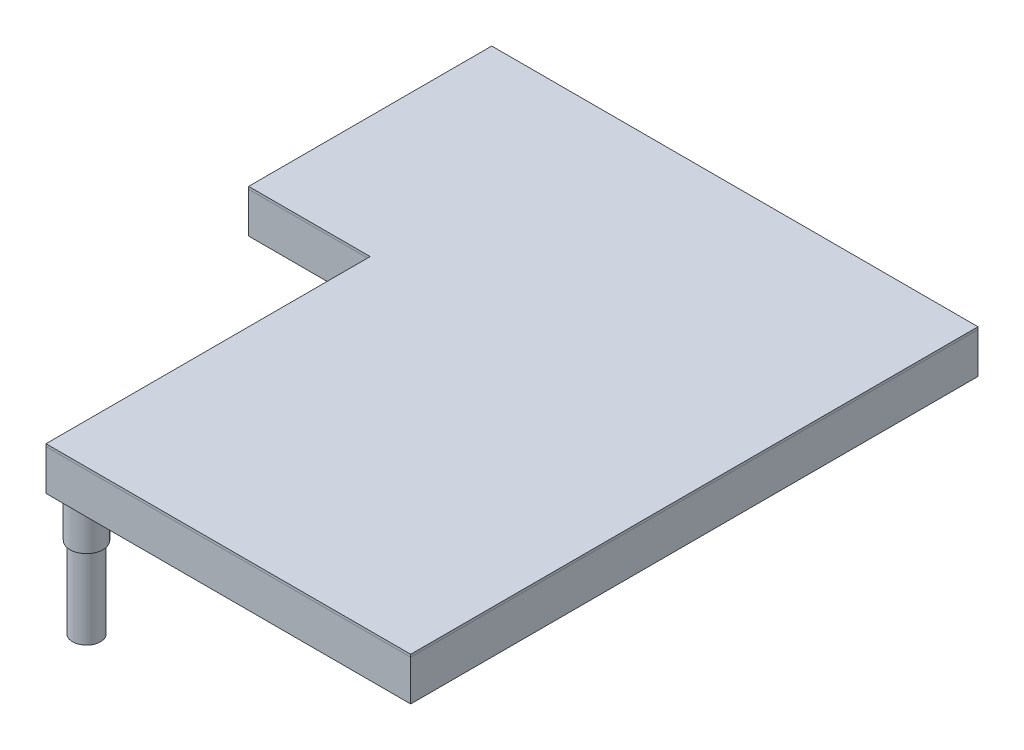
SolidWorks part; units mm, degrees
ref_plane "Front Plane" through (0, 0, 0) normal (0, 0, 1) x (1, 0, 0)
ref_plane "Top Plane" through (0, 0, 0) normal (0, 1, 0) x (1, 0, 0)
ref_plane "Right Plane" through (0, 0, 0) normal (1, 0, 0) x (0, 0, -1)
sketch "Sketch1" plane through (0, 0, 0) normal (0, 1, 0) x (1, 0, 0)
  line L0 (0, 0) -> (0, 406.4)
  line L1 (0, 406.4) -> (-152.4, 406.4)
  line L2 (-152.4, 406.4) -> (-152.4, 711.2)
  line L3 (-152.4, 711.2) -> (457.2, 711.2)
  line L4 (457.2, 711.2) -> (457.2, 0)
  line L5 (457.2, 0) -> (0, 0)
  dimension "D1" = 406.4
  dimension "D2" = 304.8
  dimension "D3" = 609.6
  dimension "D4" = 152.4
extrude "Boss-Extrude1" add sketch "Sketch1" along normal mid plane 3.175
sketch "Sketch2" plane through (0, -1.5875, 0) normal (0, -1, 0) x (1, 0, 0)
  line L0 (406.4, -50.8) -> (50.8, -50.8)
  line L1 (50.8, -50.8) -> (50.8, -457.2)
  line L2 (50.8, -457.2) -> (-101.6, -457.2)
  line L3 (-101.6, -457.2) -> (-101.6, -660.4)
  line L4 (-101.6, -660.4) -> (406.4, -660.4)
  line L5 (406.4, -660.4) -> (406.4, -50.8)
  line L6 (457.2, 0) -> (0, 0)
  line L7 (0, 0) -> (0, -406.4)
  line L8 (0, -406.4) -> (-152.4, -406.4)
  line L9 (-152.4, -406.4) -> (-152.4, -711.2)
  line L10 (-152.4, -711.2) -> (457.2, -711.2)
  line L11 (457.2, -711.2) -> (457.2, 0)
  line L12 (457.2, 0) -> (0, 0)
  line L13 (0, 0) -> (0, -406.4)
  line L14 (0, -406.4) -> (-152.4, -406.4)
  line L15 (-152.4, -406.4) -> (-152.4, -711.2)
  line L16 (-152.4, -711.2) -> (457.2, -711.2)
  line L17 (457.2, -711.2) -> (457.2, 0)
  dimension "D1" = 0
  dimension "D2" = 50.8
extrude "Boss-Extrude2" add sketch "Sketch2" along normal blind 50.8 separate body
sketch "Sketch3" plane through (0, -52.3875, 0) normal (0, -1, 0) x (1, 0, 0)
  line L0 (0, 0) -> (50.8, -50.8) construction
  circle A0 centre (25.4, -25.4) radius 17.4625
  dimension "D1" = 34.925
extrude "Boss-Extrude3" add sketch "Sketch3" along normal blind 152.4
sketch "Sketch4" plane through (0, -52.3875, 0) normal (0, -1, 0) x (1, 0, 0)
  circle A0 centre (25.4, -25.4) radius 20.6375
  circle A1 centre (25.4, -25.4) radius 17.4625 construction
  circle A2 centre (25.4, -25.4) radius 17.4625
  dimension "D1" = 41.275
extrude "Boss-Extrude4" add sketch "Sketch4" along normal blind 50.8 separate body
